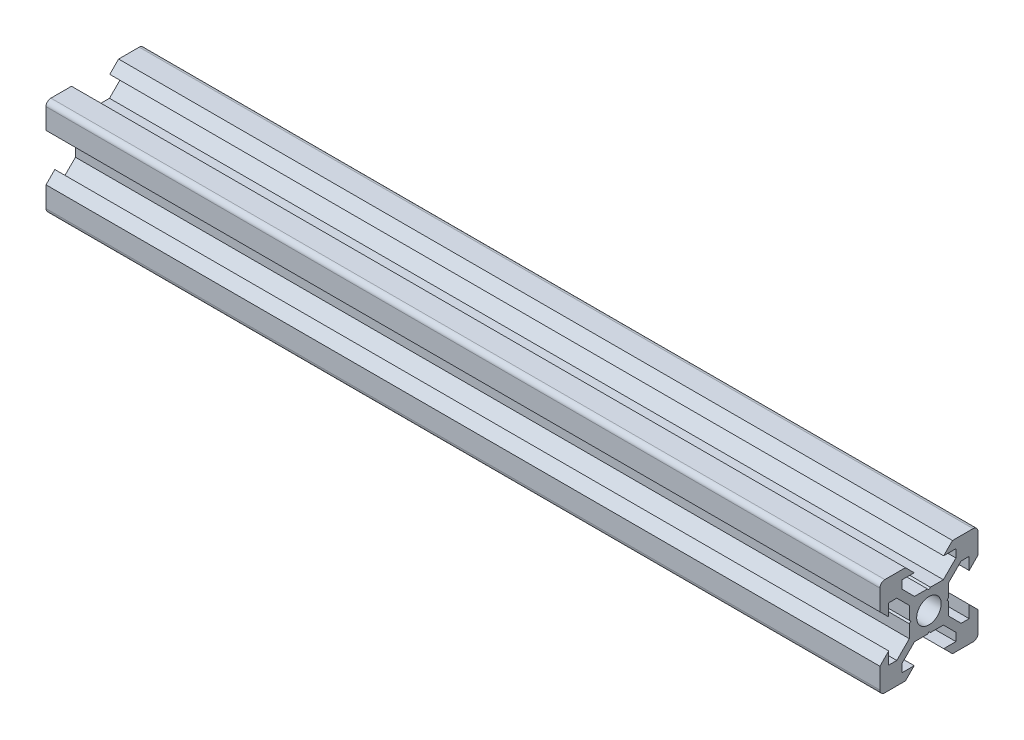
SolidWorks part; units mm, degrees
material "6063-T5"
material "6063-T5"
ref_plane "Plano frontal" through (0, 0, 0) normal (0, 0, 1) x (1, 0, 0)
ref_plane "Plano superior" through (0, 0, 0) normal (0, 1, 0) x (1, 0, 0)
ref_plane "Plano direito" through (0, 0, 0) normal (1, 0, 0) x (0, 0, -1)
sketch "Esboço1" plane through (0, 0, 0) normal (0, 0, 1) x (1, 0, 0)
  line L0 (0, 0) -> (170, 0)
  dimension "D1" = 170
other "Quadrado PF20-11 - PERFIL 2020 V-SLOT(1)"
ref_plane "Plano1" through (0, 0, 0) normal (1, 0, 0) x (0, 1, 0)
sketch "Sketch11" plane through (0, 0, 0) normal (1, 0, 0) x (0, 1, 0)
  line L0 (-4.8, 10) -> (-3, 8.2)
  line L1 (-3, 8.2) -> (-5.5, 8.2)
  line L2 (-5.5, 8.2) -> (-5.5, 6.5607)
  line L3 (-5.5, 6.5607) -> (-2.9393, 4)
  line L4 (-2.9393, 4) -> (-0.3, 4)
  line L5 (5.5, 6.5607) -> (2.9393, 4)
  line L6 (5.5, 8.2) -> (5.5, 6.5607)
  line L7 (3, 8.2) -> (5.5, 8.2)
  line L8 (4.8, 10) -> (3, 8.2)
  line L9 (-0.3, 4) -> (0, 3.7)
  line L10 (0.3, 4) -> (0, 3.7)
  line L11 (0.3, 4) -> (2.9393, 4)
  line L12 (9, 10) -> (4.8, 10)
  line L13 (10, 4.8) -> (8.2, 3)
  line L14 (10, 4.8) -> (10, 9)
  line L15 (8.2, 3) -> (8.2, 5.5)
  line L16 (8.2, 5.5) -> (6.5607, 5.5)
  line L17 (6.5607, 5.5) -> (4, 2.9393)
  line L18 (4.8, -10) -> (3, -8.2)
  line L19 (3, -8.2) -> (5.5, -8.2)
  line L20 (5.5, -8.2) -> (5.5, -6.5607)
  line L21 (5.5, -6.5607) -> (2.9393, -4)
  line L22 (2.9393, -4) -> (0.3, -4)
  line L23 (0.3, -4) -> (0, -3.7)
  line L24 (-0.3, -4) -> (0, -3.7)
  line L25 (-0.3, -4) -> (-2.9393, -4)
  line L26 (-5.5, -6.5607) -> (-2.9393, -4)
  line L27 (-5.5, -8.2) -> (-5.5, -6.5607)
  line L28 (-3, -8.2) -> (-5.5, -8.2)
  line L29 (-4.8, -10) -> (-3, -8.2)
  line L30 (-10, -4.8) -> (-10, -9)
  line L31 (-10, -4.8) -> (-8.2, -3)
  line L32 (-8.2, -3) -> (-8.2, -5.5)
  line L33 (-8.2, -5.5) -> (-6.5607, -5.5)
  line L34 (-6.5607, -5.5) -> (-4, -2.9393)
  line L35 (-4, -2.9393) -> (-4, -0.3)
  line L36 (-4, -0.3) -> (-3.7, 0)
  line L37 (-4, 0.3) -> (-3.7, 0)
  line L38 (-4, 0.3) -> (-4, 2.9393)
  line L39 (-6.5607, 5.5) -> (-4, 2.9393)
  line L40 (-8.2, 5.5) -> (-6.5607, 5.5)
  line L41 (-8.2, 3) -> (-8.2, 5.5)
  line L42 (-10, 4.8) -> (-8.2, 3)
  line L43 (-4.8, 10) -> (-9, 10)
  line L44 (4, 2.9393) -> (4, 0.3)
  line L45 (4, 0.3) -> (3.7, 0)
  line L46 (4, -0.3) -> (3.7, 0)
  line L47 (4, -0.3) -> (4, -2.9393)
  line L48 (6.5607, -5.5) -> (4, -2.9393)
  line L49 (8.2, -5.5) -> (6.5607, -5.5)
  line L50 (8.2, -3) -> (8.2, -5.5)
  line L51 (10, -4.8) -> (8.2, -3)
  line L52 (10, -9) -> (10, -4.8)
  line L53 (4.8, -10) -> (9, -10)
  line L106 (-10, 9) -> (-10, 4.8)
  line L107 (-9, -10) -> (-4.8, -10)
  arc A0 (10, 9) -> (9, 10) centre (9, 9) ccw
  arc A1 (9, -10) -> (10, -9) centre (9, -9) ccw
  arc A3 (-10, -9) -> (-9, -10) centre (-9, -9) ccw
  arc A4 (-9, 10) -> (-10, 9) centre (-9, 9) ccw
  circle A7 centre (0, 0) radius 2.5
  point P1 (-10, 10)
  point P3 (10, 10)
  point P4 (10, -10)
  point P68 (0, 0)
  point P70 (10, 0)
  point P71 (0, 0)
  point P72 (0, 0)
  point P113 (0, -10)
  point P114 (-10, -10)
  point P115 (-10, 0)
  point P116 (0, 10)
  point P118 (0, 0)
